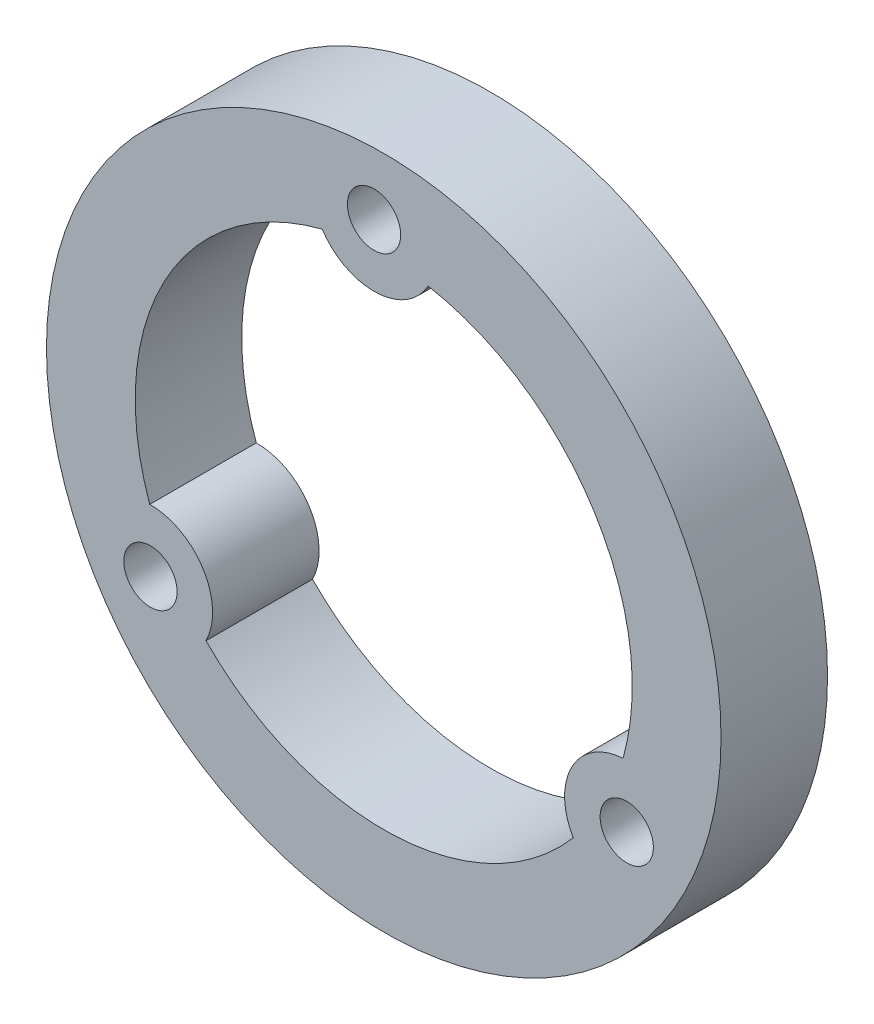
SolidWorks part; units mm, degrees
ref_plane "Plan de face" through (0, 0, 0) normal (0, 0, 1) x (1, 0, 0)
ref_plane "Plan de dessus" through (0, 0, 0) normal (0, 1, 0) x (1, 0, 0)
ref_plane "Plan de droite" through (0, 0, 0) normal (1, 0, 0) x (0, 0, -1)
sketch "Esquisse1" plane through (0, 0, 0) normal (0, 0, 1) x (1, 0, 0)
  line L0 (-0.5467, 15.4904) -> (-13.1417, -8.2186) construction
  line L1 (-13.1417, -8.2186) -> (13.6884, -7.2717) construction
  line L2 (13.6884, -7.2717) -> (-0.5467, 15.4904) construction
  circle A0 centre (0, 0) radius 19
  circle A2 centre (-0.5467, 15.4904) radius 1.5
  circle A3 centre (-13.1417, -8.2186) radius 1.5
  circle A4 centre (13.6884, -7.2717) radius 1.5
  arc A5 (-3.4686, 13.5635) -> (2.5037, 13.7743) centre (-0.5467, 15.4904) ccw
  arc A6 (-10.0121, -9.7856) -> (-13.1808, -4.7189) centre (-13.1417, -8.2186) ccw
  arc A7 (13.4806, -3.7779) -> (10.677, -9.0554) centre (13.6884, -7.2717) ccw
  arc A8 (-10.0121, -9.7856) -> (10.677, -9.0554) centre (0, 0) ccw
  arc A9 (-3.4686, 13.5635) -> (-13.1808, -4.7189) centre (0, 0) ccw
  arc A10 (13.4806, -3.7779) -> (2.5037, 13.7743) centre (0, 0) ccw
  circle A11 centre (0, 0) radius 14 construction
  dimension "D1" = 38
  dimension "D3" = 3
  dimension "D4" = 3
  dimension "D5" = 3
  dimension "D8" = 15.5
  dimension "D9" = 15.5
  dimension "D10" = 15.5
  dimension "D11" = 7
  dimension "D12" = 7
  dimension "D13" = 7
  dimension "D6" = 60
  dimension "D7" = 60
extrude "Boss.-Extru.2" add sketch "Esquisse1" along normal blind 6
